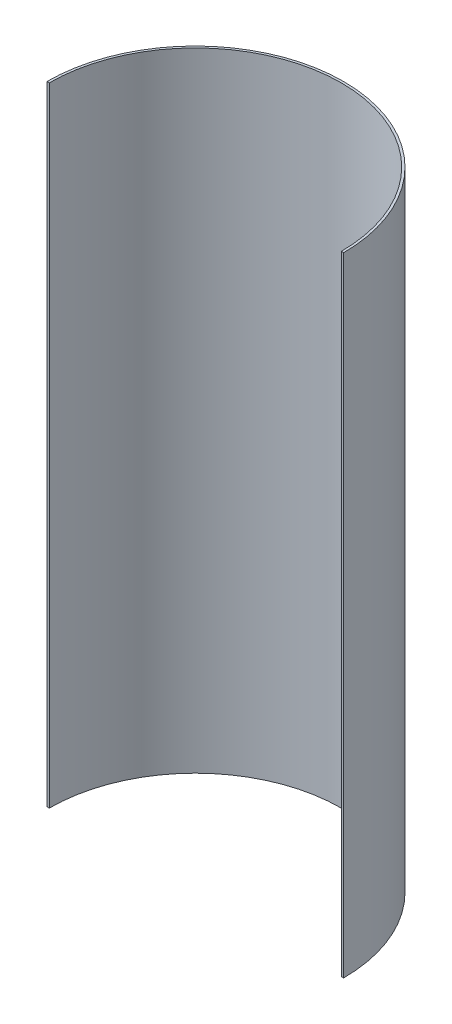
SolidWorks part; units mm, degrees
ref_plane "Front Plane" through (0, 0, 0) normal (0, 0, 1) x (1, 0, 0)
ref_plane "Top Plane" through (0, 0, 0) normal (0, 1, 0) x (1, 0, 0)
ref_plane "Right Plane" through (0, 0, 0) normal (1, 0, 0) x (0, 0, -1)
sketch "Sketch1" plane through (0, 0, 0) normal (0, 1, 0) x (1, 0, 0)
  arc A0 (-158.7696, 98.9209) -> (165.0804, 98.9209) centre (3.1554, 98.9209) cw
  dimension "D1" = 161.925
extrude "Extrude-Thin1" add sketch "Sketch1" along normal blind 685.8 thin
